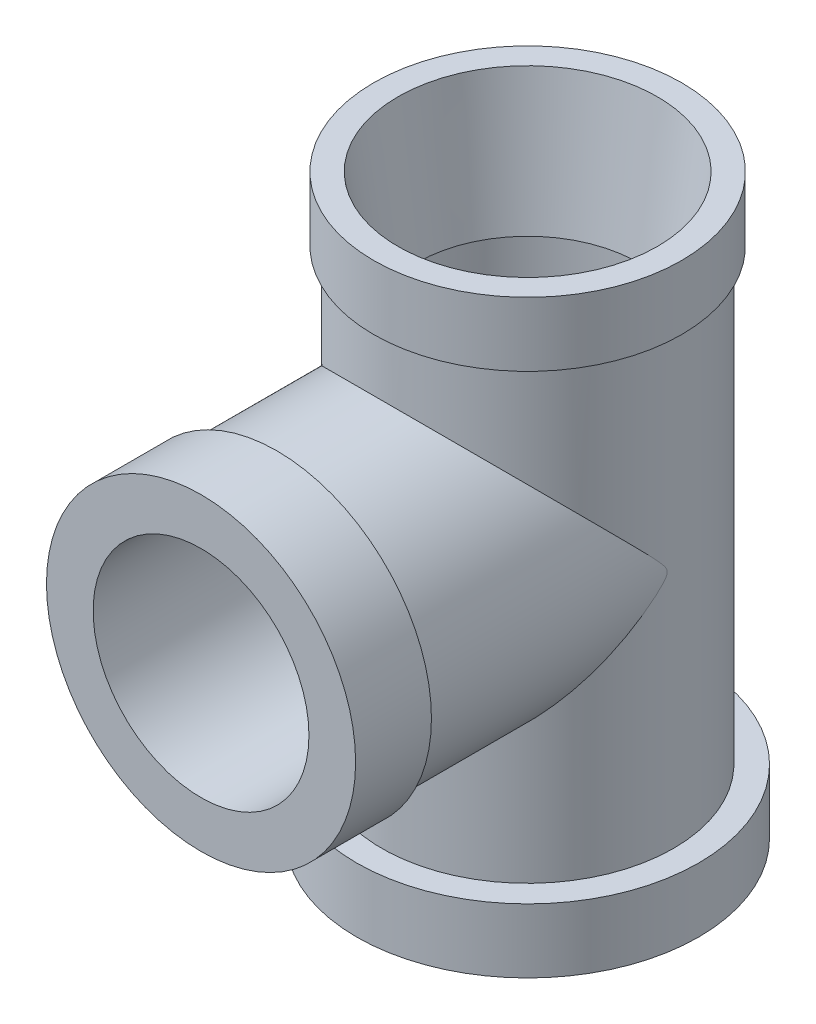
SolidWorks part; units mm, degrees
ref_plane "Alzado" through (0, 0, 0) normal (0, 0, 1) x (1, 0, 0)
ref_plane "Planta" through (0, 0, 0) normal (0, 1, 0) x (1, 0, 0)
ref_plane "Vista lateral" through (0, 0, 0) normal (1, 0, 0) x (0, 0, -1)
sketch "Croquis1" plane through (0, 0, 0) normal (0, 0, 1) x (1, 0, 0)
  line L0 (0, 29.9363) -> (0, -31.1161) construction
  line L1 (11.12, 18.7889) -> (13.2, 18.7889)
  line L2 (13.2, 18.7889) -> (13.2, 13.2889)
  line L3 (13.2, 13.2889) -> (12.5, 13.2889)
  line L4 (12.5, 13.2889) -> (12.5, -25.2111)
  line L5 (12.5, -25.2111) -> (14.6593, -25.2111)
  line L6 (14.6593, -25.2111) -> (14.6593, -30.7111)
  line L7 (14.6593, -30.7111) -> (11.12, -30.7111)
  line L8 (11.12, -30.7111) -> (9.525, -16.2521)
  line L9 (9.525, 7.2548) -> (10.3159, 7.2548)
  line L10 (9.525, 7.2548) -> (11.12, 18.7889)
  line L11 (10.3159, 7.2548) -> (10.3159, -16.2521)
  line L12 (10.3159, -16.2521) -> (9.525, -16.2521)
  dimension "D1" = 13.2
  dimension "D2" = 5.5
  dimension "D3" = 12.5
  dimension "D4" = 5.5
  dimension "D5" = 11.12
  dimension "D6" = 9.525
revolve "Revolución1" add sketch "Croquis1" angle 360 about L0
sketch "Croquis2" plane through (0, 0, 0) normal (0, 0, 1) x (1, 0, 0)
  line L0 (0, 24.8044) -> (0, -33.6806) construction
  circle A0 centre (0, -4.4381) radius 12.489
extrude "Saliente-Extruir1" add sketch "Croquis2" along normal blind 28
sketch "Croquis3" plane through (0, 0, 0) normal (0, 1, 0) x (1, 0, 0)
  circle A0 centre (0, 0) radius 9
extrude "Cortar-Extruir1" cut sketch "Croquis3" against normal through all both and the other way through all
sketch "Croquis4" plane through (0, 0, 28) normal (0, 0, 1) x (1, 0, 0)
  circle A0 centre (0, -4.4381) radius 13.25
  dimension "D1" = 26.5
extrude "Saliente-Extruir2" add sketch "Croquis4" against normal blind 6.5
sketch "Croquis5" plane through (0, 0, 28) normal (0, 0, 1) x (1, 0, 0)
  circle A0 centre (0, -4.4381) radius 9.25
  dimension "D1" = 18.5
extrude "Cortar-Extruir2" cut sketch "Croquis5" against normal up to next
